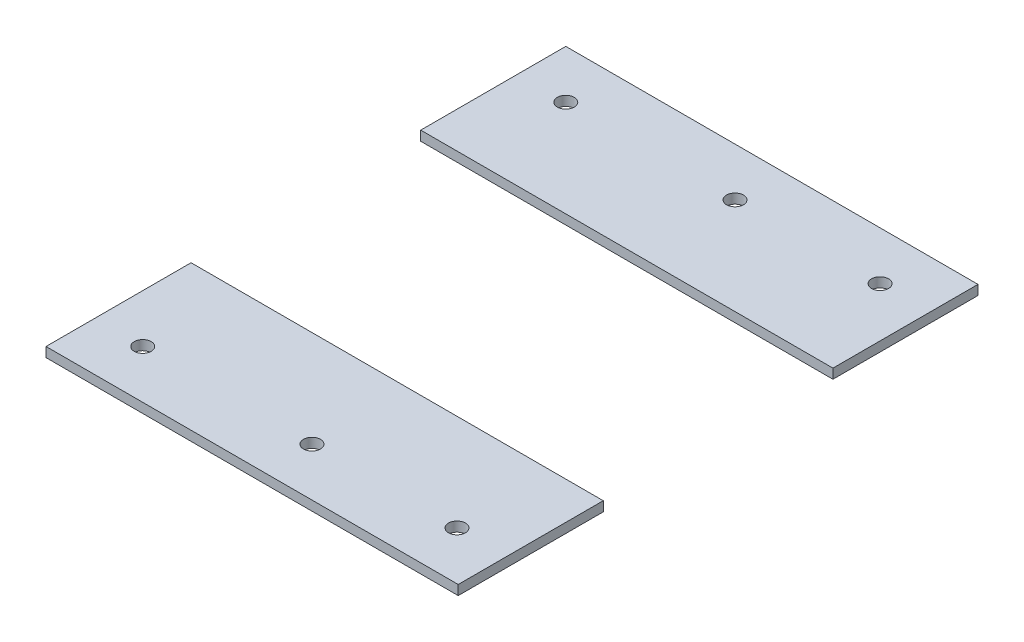
SolidWorks part; units mm, degrees
ref_plane "Front Plane" through (0, 0, 0) normal (0, 0, 1) x (1, 0, 0)
ref_plane "Top Plane" through (0, 0, 0) normal (0, 1, 0) x (1, 0, 0)
ref_plane "Right Plane" through (0, 0, 0) normal (1, 0, 0) x (0, 0, -1)
sketch "Sketch1" plane through (0, 0, 0) normal (0, 1, 0) x (1, 0, 0)
  line L1 (0, 205) -> (170.5, 205)
  line L2 (0, 205) -> (0, -10)
  line L3 (0, -10) -> (170.5, -10)
  line L4 (170.5, 205) -> (170.5, -10)
  circle A0 centre (20, 10) radius 3.5
  circle A1 centre (150, 10) radius 3.5
  circle A2 centre (90, 10) radius 3.5
  circle A3 centre (20, 185) radius 3.5
  circle A4 centre (90, 185) radius 3.5
  circle A5 centre (150, 185) radius 3.5
extrude "Boss-Extrude1" add sketch "Sketch1" along normal blind 4
sketch "Sketch2" plane through (0, 0, 0) normal (0, -1, 0) x (1, 0, 0)
  line L1 (194.4674, -50) -> (-25, -50)
  line L2 (194.4674, -50) -> (194.4674, -145)
  line L3 (194.4674, -145) -> (-25, -145)
  line L4 (-25, -50) -> (-25, -145)
extrude "Cut-Extrude1" cut sketch "Sketch2" against normal blind 10
